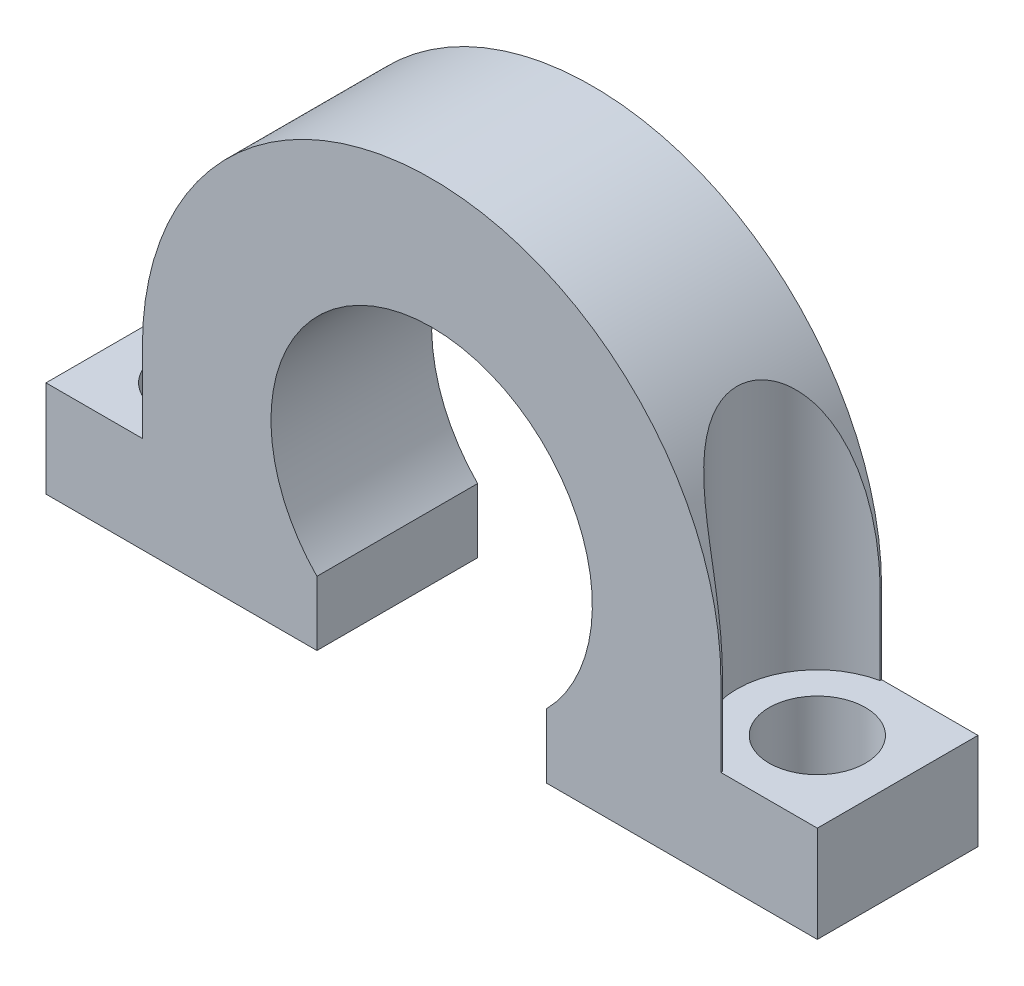
SolidWorks part; units mm, degrees
ref_plane "Plano frontal" through (0, 0, 0) normal (0, 0, 1) x (1, 0, 0)
ref_plane "Plano superior" through (0, 0, 0) normal (0, 1, 0) x (1, 0, 0)
ref_plane "Plano direito" through (0, 0, 0) normal (1, 0, 0) x (0, 0, -1)
sketch "Esboço1" plane through (0, 0, 0) normal (0, 0, 1) x (1, 0, 0)
  line L1 (-9, -2.5) -> (-9, 0)
  line L11 (12, -5.5) -> (12, -2.5)
  line L12 (12, -5.5) -> (3.5707, -5.5)
  line L13 (12, -2.5) -> (9, -2.5)
  line L14 (9, 0) -> (9, -2.5)
  line L15 (3.5707, -5.5) -> (3.5707, -3.5)
  line L16 (-3.5707, -3.5) -> (-3.5707, -5.5)
  line L17 (-12, -5.5) -> (-3.5707, -5.5)
  line L18 (-12, -5.5) -> (-12, -2.5)
  line L19 (-9, -2.5) -> (-12, -2.5)
  arc A0 (-9, 0) -> (9, 0) centre (0, 0) cw
  arc A1 (-3.5707, -3.5) -> (3.5707, -3.5) centre (0, 0) cw
  dimension "D1" = 5.5
  dimension "D4" = 24
  dimension "D5" = 5
  dimension "D3" = 4
  dimension "D2" = 3
  dimension "D6" = 2
extrude "Ressalto-extrusão1" add sketch "Esboço1" along normal blind 5 contours L1 A0 L14 L13 L11 L12 L15 A1 L16 L17 L18 L19
sketch "Esboço2" plane through (0, -2.5, 0) normal (0, 1, 0) x (1, 0, 0)
  line L0 (-12, -5) -> (-12, 0) construction
  circle A0 centre (-9.5, -2.5) radius 1.5
  circle A1 centre (9.5, -2.5) radius 1.5
  point P7 (-12, -2.5)
  dimension "D1" = 3
  dimension "D2" = 2.5
  dimension "D4" = 19
extrude "Corte-extrusão1" cut sketch "Esboço2" against normal through all both and the other way through all
sketch "Esboço3" plane through (0, -2.5, 0) normal (0, 1, 0) x (1, 0, 0)
  circle A0 centre (-9.5, -2.5) radius 2.5
  circle A1 centre (9.5, -2.5) radius 2.5
  dimension "D1" = 5
  dimension "D2" = 5
extrude "Corte-extrusão2" cut sketch "Esboço3" along normal through all
